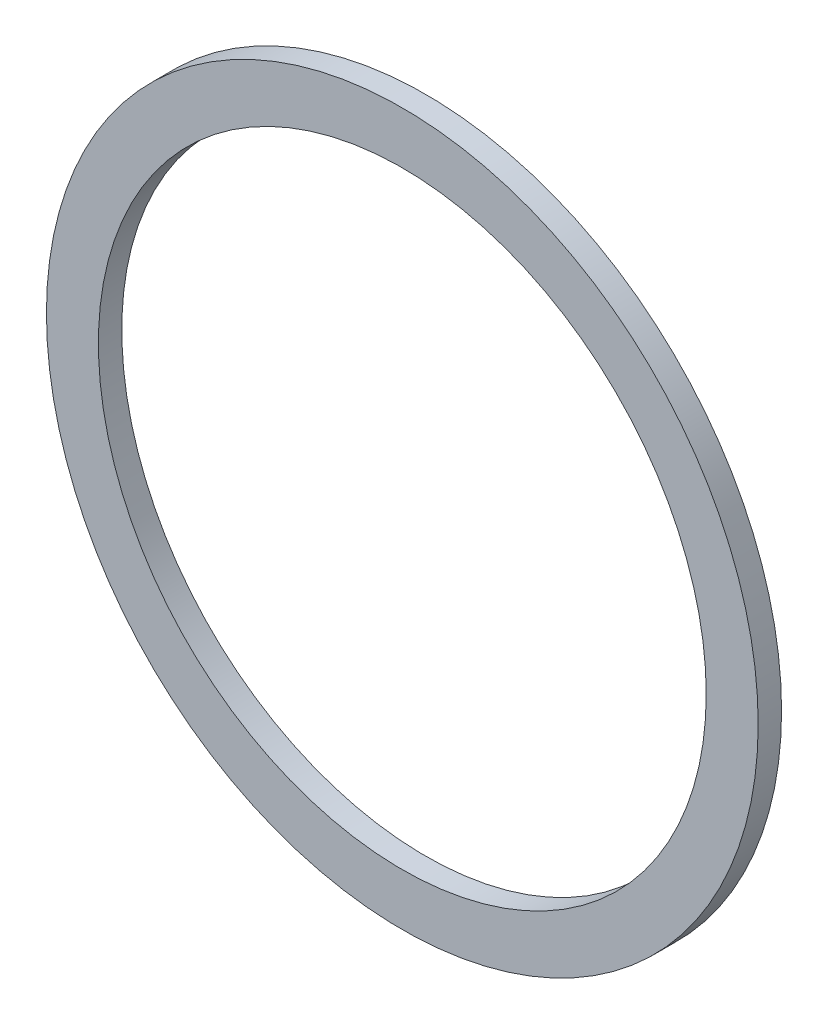
SolidWorks part; units mm, degrees
ref_plane "Front Plane" through (0, 0, 0) normal (0, 0, 1) x (1, 0, 0)
ref_plane "Top Plane" through (0, 0, 0) normal (0, 1, 0) x (1, 0, 0)
ref_plane "Right Plane" through (0, 0, 0) normal (1, 0, 0) x (0, 0, -1)
sketch "Sketch1" plane through (0, 0, 0) normal (0, 0, 1) x (1, 0, 0)
  circle A0 centre (0, 0) radius 23.4
  circle A1 centre (0, 0) radius 27.4
  dimension "D1" = 54.8
  dimension "D2" = 46.8
extrude "Boss-Extrude1" add sketch "Sketch1" along normal blind 1.8
